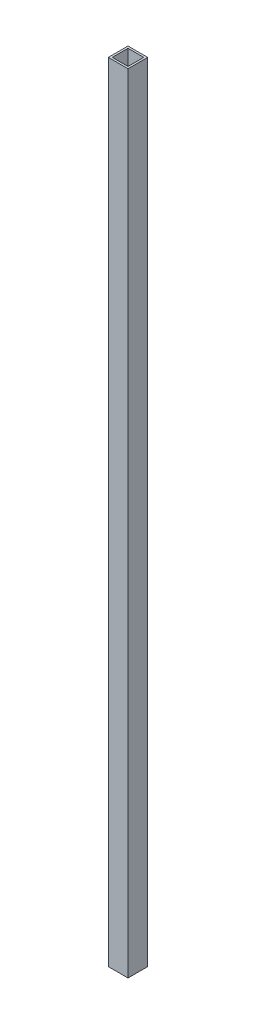
SolidWorks part; units mm, degrees
material "AISI 1020"
ref_plane "Front Plane" through (0, 0, 0) normal (0, 0, 1) x (1, 0, 0)
ref_plane "Top Plane" through (0, 0, 0) normal (0, 1, 0) x (1, 0, 0)
ref_plane "Right Plane" through (0, 0, 0) normal (1, 0, 0) x (0, 0, -1)
sketch "Sketch1" plane through (0, 0, 0) normal (0, 0, 1) x (1, 0, 0)
  line L1 (-31.7391, 49.7826) -> (-11.7391, 49.7826)
  line L2 (-31.7391, 49.7826) -> (-31.7391, -750.2174)
  line L3 (-31.7391, -750.2174) -> (-11.7391, -750.2174)
  line L4 (-11.7391, 49.7826) -> (-11.7391, -750.2174)
  dimension "D1" = 20
  dimension "D2" = 800
extrude "Boss-Extrude1" add sketch "Sketch1" against normal blind 20
sketch "Sketch2" plane through (0, 49.7826, 0) normal (0, 1, 0) x (1, 0, 0)
  line L8 (-29.7391, 2) -> (-13.7391, 2)
  line L9 (-13.7391, 2) -> (-13.7391, 18)
  line L10 (-13.7391, 18) -> (-29.7391, 18)
  line L11 (-29.7391, 18) -> (-29.7391, 2)
  line L12 (-29.7391, 2) -> (-13.7391, 2)
  line L13 (-13.7391, 2) -> (-13.7391, 18)
  line L14 (-13.7391, 18) -> (-29.7391, 18)
  line L15 (-29.7391, 18) -> (-29.7391, 2)
  dimension "D1" = 2
extrude "Cut-Extrude1" cut sketch "Sketch2" against normal blind 200
